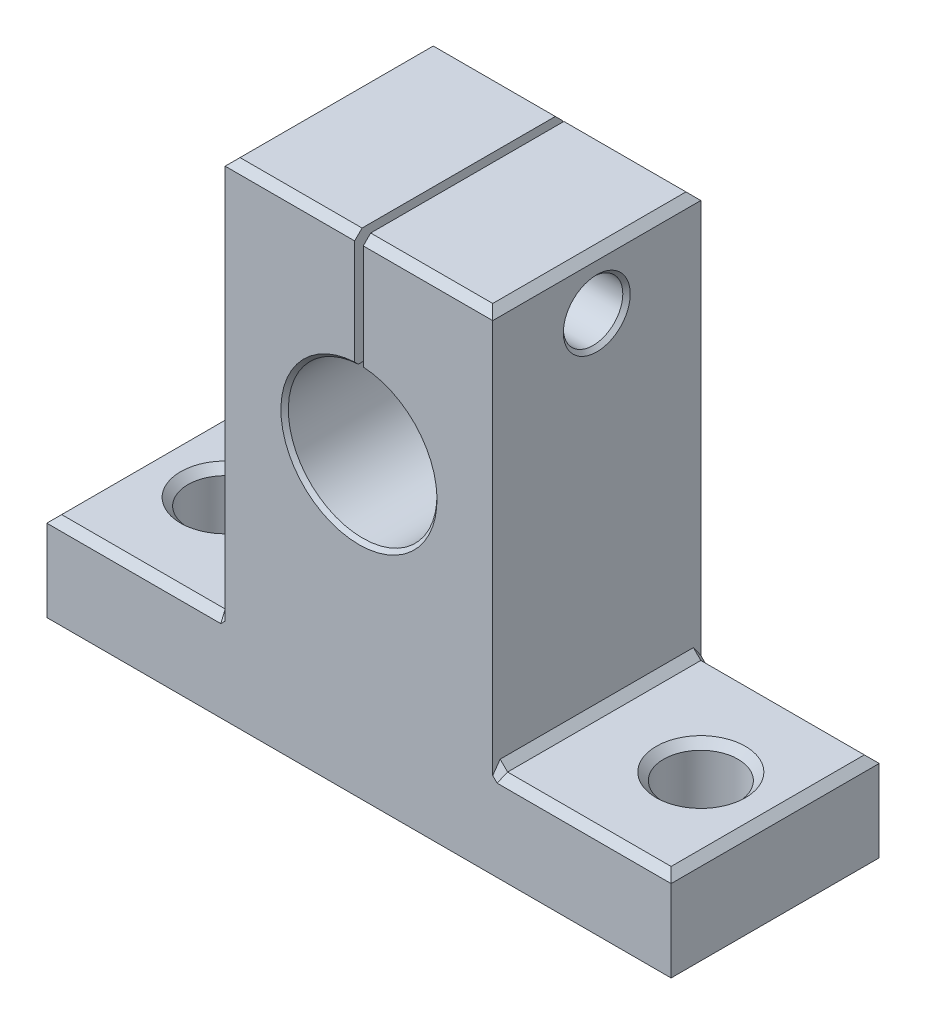
SolidWorks part; units mm, degrees
ref_plane "Front Plane" through (0, 0, 0) normal (0, 0, 1) x (1, 0, 0)
ref_plane "Top Plane" through (0, 0, 0) normal (0, 1, 0) x (1, 0, 0)
ref_plane "Right Plane" through (0, 0, 0) normal (1, 0, 0) x (0, 0, -1)
sketch "Sketch1" plane through (0, 0, 0) normal (0, 0, 1) x (1, 0, 0)
  line L0 (-0.4211, -3.746) -> (-0.4211, 23.054)
  line L1 (-12.4211, -3.746) -> (-0.4211, -3.746)
  line L2 (-12.4211, -3.746) -> (-12.4211, -9.746)
  line L3 (-12.4211, -9.746) -> (29.5789, -9.746)
  line L4 (29.5789, -3.746) -> (29.5789, -9.746)
  line L5 (-0.4211, 23.054) -> (17.5789, 23.054)
  line L6 (17.5789, 23.054) -> (17.5789, -3.746)
  line L7 (17.5789, -3.746) -> (29.5789, -3.746)
  dimension "D1" = 6
  dimension "D2" = 42
  dimension "D3" = 18
  dimension "D4" = 32.8
  dimension "D5" = 12
extrude "Boss-Extrude1" add sketch "Sketch1" along normal blind 14 contours L3 L4 L7 L6 L5 L0 L1 L2
chamfer "Chamfer1" distance 0.5 angle 45 1 edges at (17.5789, -3.746, 7)
chamfer "Chamfer2" distance 0.5 angle 45 1 edges at (-0.4211, -3.746, 7)
chamfer "Chamfer3" distance 0.5 angle 45 1 edges at (-12.4211, -3.746, 7)
chamfer "Chamfer4" distance 0.5 angle 45 1 edges at (29.5789, -3.746, 7)
chamfer "Chamfer5" distance 0.5 angle 45 1 edges at (17.5789, 23.054, 7)
chamfer "Chamfer6" distance 0.5 angle 45 1 edges at (-0.4211, 23.054, 7)
sketch "Sketch2" plane through (0, 0, 14) normal (0, 0, 1) x (1, 0, 0)
  line L0 (8.5789, 23.054) -> (8.5789, -12.1727) construction
  line L1 (-5.2909, 10.254) -> (23.3797, 10.254) construction
  line L2 (-12.4211, -9.746) -> (29.5789, -9.746) construction
  circle A0 centre (8.5789, 10.254) radius 5
  dimension "D1" = 20
extrude "Cut-Extrude2" cut sketch "Sketch2" against normal blind 14
sketch "Sketch3" plane through (0, 0, 14) normal (0, 0, 1) x (1, 0, 0)
  line L0 (8.5789, 15.254) -> (8.5789, 26.1093) construction
  line L1 (8.2886, 23.332) -> (8.2886, 14.5431)
  line L2 (8.8693, 23.332) -> (8.8693, 14.9731)
  line L3 (8.8693, 14.9731) -> (8.2886, 14.5431)
  line L4 (8.2886, 23.332) -> (8.8693, 23.332)
  point P4 (8.8693, 23.332)
extrude "Cut-Extrude3" cut sketch "Sketch3" against normal blind 14
sketch "Sketch4" plane through (17.5789, 0, 0) normal (1, 0, 0) x (0, 0, -1)
  line L0 (-7, 22.554) -> (-7, -12.5451) construction
  line L1 (-7, -12.5451) -> (-7, 34.8548) construction
  circle A0 centre (-7, 19.4811) radius 2
extrude "Cut-Extrude4" cut sketch "Sketch4" against normal blind 25
sketch "Sketch5" plane through (0, -9.746, 0) normal (0, -1, 0) x (1, 0, 0)
  line L0 (-12.4211, 7) -> (32.5725, 7) construction
  line L1 (32.5725, 7) -> (-14.7699, 7) construction
  line L2 (8.5789, 14) -> (8.5789, 0) construction
  line L3 (8.5789, 0) -> (8.5789, 20.056) construction
  circle A0 centre (-7.4211, 7) radius 2.5
  circle A1 centre (24.5789, 7) radius 2.5
  dimension "D1" = 32
  dimension "D2" = 16
extrude "Cut-Extrude5" cut sketch "Sketch5" against normal blind 25
chamfer "Chamfer7" distance 0.5 angle 45 1 edges at (-9.9211, -3.746, 7)
chamfer "Chamfer8" distance 0.5 angle 45 1 edges at (22.0789, -3.746, 7)
chamfer "Chamfer9" distance 0.5 angle 45 1 edges at (23.5789, -3.746, 14)
chamfer "Chamfer10" distance 0.5 angle 45 1 edges at (18.0789, -3.746, 14)
chamfer "Chamfer11" distance 0.5 angle 45 1 edges at (23.5789, -3.746, 0)
chamfer "Chamfer12" distance 0.5 angle 45 1 edges at (18.0789, -3.746, 0)
chamfer "Chamfer13" distance 0.5 angle 45 2 edges at (4.1837, 23.054, 0) (12.9741, 23.054, 0)
chamfer "Chamfer14" distance 0.5 angle 45 2 edges at (12.9741, 23.054, 14) (4.1837, 23.054, 14)
chamfer "Chamfer15" distance 0.5 angle 45 4 edges at (-0.6711, -3.496, 0) (-6.4211, -3.746, 0) (-0.6711, -3.496, 14) (-6.4211, -3.746, 14)
chamfer "Chamfer16" distance 0.25 angle 45 2 edges at (8.5789, 5.254, 14) (8.5789, 5.254, 0)
chamfer "Chamfer17" distance 0.25 angle 45 1 edges at (-0.4211, 17.4811, 7)
chamfer "Chamfer18" distance 0.25 angle 45 1 edges at (17.5789, 21.4811, 7)
